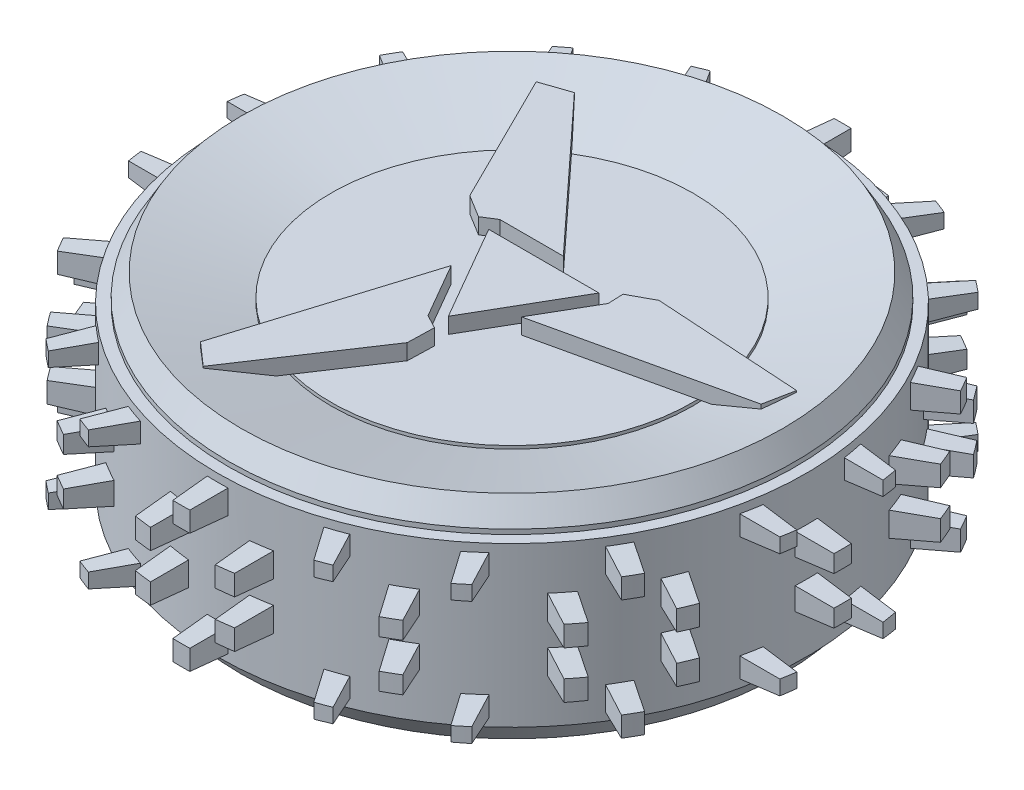
SolidWorks part; units mm, degrees
ref_plane "前视基准面" through (0, 0, 0) normal (0, 0, 1) x (1, 0, 0)
ref_plane "上视基准面" through (0, 0, 0) normal (0, 1, 0) x (1, 0, 0)
ref_plane "右视基准面" through (0, 0, 0) normal (1, 0, 0) x (0, 0, -1)
other "Configuration Table"
sketch "草图1" plane through (0, 0, 0) normal (0, 1, 0) x (1, 0, 0)
  circle A0 centre (0, 0) radius 90
  dimension "D1" = 180
extrude "凸台-拉伸1" add sketch "草图1" along normal mid plane 67.5
chamfer "倒角1" distance 7 angle 30 1 edges at (0, 33.75, 90)
chamfer "倒角2" distance 7 angle 30 1 edges at (0, -33.75, 90)
sketch "草图2" plane through (0, 0, 0) normal (0, 1, 0) x (1, 0, 0)
  circle A0 centre (0, 0) radius 93.5
  dimension "D1" = 187
extrude "凸台-拉伸2" add sketch "草图2" along normal mid plane 50.5
ref_plane "基准面1" through (0, 0, 80) normal (0, 0, 1) x (1, 0, 0)
ref_plane "基准面2" through (0, 0, 110) normal (0, 0, 1) x (1, 0, 0)
sketch "草图4" plane through (0, 0, 80) normal (0, 0, 1) x (1, 0, 0)
  line L0 (0, -55) -> (0, 55) construction
  line L1 (-4, 23.5) -> (4, 23.5)
  line L2 (-4, 23.5) -> (-4, 14.5)
  line L3 (-4, 14.5) -> (4, 14.5)
  line L4 (4, 23.5) -> (4, 14.5)
  line L5 (-17, 12) -> (-9, 12)
  line L6 (-17, 12) -> (-17, 3)
  line L7 (-17, 3) -> (-9, 3)
  line L8 (-9, 12) -> (-9, 3)
  line L9 (9, 12) -> (9, 3)
  line L10 (17, 3) -> (9, 3)
  line L11 (17, 12) -> (17, 3)
  line L12 (17, 12) -> (9, 12)
  line L13 (55, 0) -> (-55, 0) construction
  line L14 (17, -12) -> (9, -12)
  line L15 (17, -12) -> (17, -3)
  line L16 (17, -3) -> (9, -3)
  line L17 (9, -12) -> (9, -3)
  line L18 (-9, -12) -> (-9, -3)
  line L19 (-17, -3) -> (-9, -3)
  line L20 (-17, -12) -> (-17, -3)
  line L21 (-17, -12) -> (-9, -12)
  line L22 (4, -23.5) -> (4, -14.5)
  line L23 (-4, -14.5) -> (4, -14.5)
  line L24 (-4, -23.5) -> (-4, -14.5)
  line L25 (-4, -23.5) -> (4, -23.5)
  point P29 (0, 14.5)
  dimension "D1" = 6
  dimension "D2" = 24
  dimension "D3" = 34
  dimension "D4" = 18
  dimension "D5" = 47
extrude "凸台-拉伸3" add sketch "草图4" along normal mid plane 50.5 draft 3
ref_plane "基准面3" through (80, 0, 0) normal (1, 0, 0) x (0, 0, -1)
sketch "草图5" plane through (80, 0, 0) normal (1, 0, 0) x (0, 0, -1)
  line L0 (0, 55) -> (0, -55) construction
  line L1 (-20, 23.5) -> (-12, 23.5)
  line L2 (-20, 23.5) -> (-20, 15.5742)
  line L3 (-20, 15.5742) -> (-12, 15.5742)
  line L4 (-12, 23.5) -> (-12, 15.5742)
  line L9 (-4.5, 12) -> (4.5, 12)
  line L10 (-4.5, 12) -> (-4.5, 3)
  line L11 (-4.5, 3) -> (4.5, 3)
  line L12 (4.5, 12) -> (4.5, 3)
  line L13 (12, 23.5) -> (12, 15.5742)
  line L14 (20, 15.5742) -> (12, 15.5742)
  line L15 (20, 23.5) -> (20, 15.5742)
  line L16 (20, 23.5) -> (12, 23.5)
  line L17 (55, 0) -> (-55, 0) construction
  line L18 (20, -23.5) -> (12, -23.5)
  line L19 (20, -23.5) -> (20, -15.5742)
  line L20 (20, -15.5742) -> (12, -15.5742)
  line L21 (12, -23.5) -> (12, -15.5742)
  line L22 (4.5, -12) -> (4.5, -3)
  line L23 (-4.5, -3) -> (4.5, -3)
  line L24 (-4.5, -12) -> (-4.5, -3)
  line L25 (-4.5, -12) -> (4.5, -12)
  line L26 (-12, -23.5) -> (-12, -15.5742)
  line L27 (-20, -15.5742) -> (-12, -15.5742)
  line L28 (-20, -23.5) -> (-20, -15.5742)
  line L29 (-20, -23.5) -> (-12, -23.5)
  point P28 (0, 12)
  dimension "D1" = 40
  dimension "D2" = 47
  dimension "D3" = 6
  dimension "D4" = 24
  dimension "D5" = 24
extrude "凸台-拉伸4" add sketch "草图5" along normal mid plane 50.5 draft 4
pattern_circular "阵列(圆周)1" count 6 over 360 about axis through (0, 0, 0) along (0, 1, 0) of "凸台-拉伸4"
pattern_circular "阵列(圆周)2" count 6 over 360 about axis through (0, 0, 0) along (0, 1, 0) of "凸台-拉伸3"
sketch "草图6" plane through (0, 0, 0) normal (0, 1, 0) x (1, 0, 0)
  circle A0 centre (0, 0) radius 105
  circle A1 centre (0, 0) radius 115
  dimension "D1" = 210
  dimension "D2" = 10
extrude "切除-拉伸1" cut sketch "草图6" against normal through all and the other way through all
ref_plane "基准面4" through (0, -26.75, 0) normal (0, -1, 0) x (-1, 0, 0)
sketch "草图7" plane through (0, 0, 0) normal (0, 0, 1) x (1, 0, 0)
  line L0 (-85.9585, 33.75) -> (-57.5, 25.75)
  line L1 (-57.5, 25.75) -> (-57.5, 26.75)
  line L2 (-57.5, 26.75) -> (57.5, 26.75) construction
  line L3 (0, 26.75) -> (0, 33.75)
  line L4 (85.9585, 33.75) -> (-85.9585, 33.75) construction
  line L5 (0, -37.125) -> (0, 37.125) construction
  line L6 (57.5, 25.75) -> (57.5, 26.75) construction
  line L7 (85.9585, 33.75) -> (57.5, 25.75) construction
  line L8 (-85.9585, 33.75) -> (0, 33.75)
  line L9 (-57.5, 26.75) -> (0, 26.75)
  dimension "D1" = 7
  dimension "D2" = 1
  dimension "D3" = 115
revolve "切除-旋转1" cut sketch "草图7" angle 360 about L3
sketch "草图8" plane through (0, 26.75, 0) normal (0, 1, 0) x (1, 0, 0)
  line L0 (-17.5, 10.1036) -> (17.5, 10.1036)
  line L1 (17.5, 10.1036) -> (0, -20.2073)
  line L2 (0, -20.2073) -> (-17.5, 10.1036)
  line L3 (0, 0) -> (-17.5, 10.1036) construction
  line L4 (0, 0) -> (17.5, 10.1036) construction
  line L5 (0, 0) -> (0, -20.2073) construction
  line L6 (-18.4387, 14.5799) -> (1.715, 14.5799)
  line L7 (1.715, 14.5799) -> (-41.4802, 61.2865)
  line L8 (-41.4802, 61.2865) -> (-50.5383, 58.2184)
  line L9 (-50.5383, 58.2184) -> (-29.7781, 16.3754)
  line L10 (-29.7781, 16.3754) -> (-22.596, 11.9557)
  line L11 (-22.596, 11.9557) -> (-18.4387, 14.5799)
  line L12 (21.6519, 13.5909) -> (21.8459, 8.6784)
  line L13 (21.8459, 8.6784) -> (11.769, -8.7752)
  line L14 (11.769, -8.7752) -> (73.8157, 5.2797)
  line L15 (73.8157, 5.2797) -> (75.6878, 14.6583)
  line L16 (75.6878, 14.6583) -> (29.0706, 17.6008)
  line L17 (29.0706, 17.6008) -> (21.6519, 13.5909)
  line L18 (0.9441, -25.5465) -> (-3.4072, -23.2583)
  line L19 (-3.4072, -23.2583) -> (-13.4841, -5.8047)
  line L20 (-13.4841, -5.8047) -> (-32.3355, -66.5662)
  line L21 (-32.3355, -66.5662) -> (-25.1494, -72.8767)
  line L22 (-25.1494, -72.8767) -> (0.7075, -33.9763)
  line L23 (0.7075, -33.9763) -> (0.9441, -25.5465)
  point P5 (0, 10.1036)
  point P27 (0, 0)
  dimension "D1" = 35
  dimension "D2" = 3
extrude "凸台-拉伸5" add sketch "草图8" along normal blind 5
mirror "镜向1" about plane through (0, 0, 0) normal (0, 1, 0) of "凸台-拉伸5", "切除-旋转1"
sketch "草图9" plane through (0, -26.75, 0) normal (0, -1, 0) x (1, 0, 0)
  circle A0 centre (0, 0) radius 24.5
  circle A1 centre (0, 0) radius 30
  dimension "D1" = 49
  dimension "D2" = 60
extrude "切除-拉伸2" cut sketch "草图9" against normal blind 6 and the other way through all
sketch "草图10" plane through (0, -26.75, 0) normal (0, -1, 0) x (1, 0, 0)
  circle A0 centre (0, 0) radius 24.5
  circle A1 centre (0, 0) radius 24.5 construction
extrude "切除-拉伸3" cut sketch "草图10" along normal through all
sketch "草图11" plane through (0, -26.75, 0) normal (0, -1, 0) x (1, 0, 0)
  circle A0 centre (0, 0) radius 20 construction
  circle A1 centre (0, 20) radius 2
  circle A2 centre (17.3205, 10) radius 2
  circle A3 centre (17.3205, -10) radius 2
  circle A4 centre (0, -20) radius 2
  circle A5 centre (-17.3205, -10) radius 2
  circle A6 centre (-17.3205, 10) radius 2
  point P18 (0, 0)
  dimension "D1" = 40
  dimension "D2" = 4
  dimension "D3" = 6
extrude "切除-拉伸4" cut sketch "草图11" against normal blind 12
hole_wizard "M6 螺纹孔1" positions "3D草图1" profile "草图12" tap size "M6" standard "GB"
sketch3d "3D草图1"
  circle A0 centre (0, -26.75, 20) radius 2 construction
  circle A1 centre (-17.3205, -26.75, 10) radius 2 construction
  circle A2 centre (-17.3205, -26.75, -10) radius 2 construction
  circle A3 centre (0, -26.75, -20) radius 2 construction
  circle A4 centre (17.3205, -26.75, -10) radius 2 construction
  circle A5 centre (17.3205, -26.75, 10) radius 2 construction
  point P0 (0, -26.75, 20)
  point P2 (-17.3205, -26.75, 10)
  point P4 (-17.3205, -26.75, -10)
  point P6 (0, -26.75, -20)
  point P8 (17.3205, -26.75, -10)
  point P10 (17.3205, -26.75, 10)
  point P15 (0, -28.75, 20)
  point P19 (-17.3205, -28.75, 10)
  point P23 (-17.3205, -28.75, -10)
  point P26 (0, -28.75, -20)
  point P31 (17.3205, -28.75, -10)
  point P35 (17.3205, -28.75, 10)
sketch "草图12" plane through (0, -26.75, 20) normal (1, 0, 0) x (0, 0, -1)
  line L0 (0, 0) -> (0, 13.5022)
  line L1 (0, 13.5022) -> (2.5, 12)
  line L2 (2.5, 12) -> (2.5, 0)
  line L5 (2.5, 0) -> (0, 0)
  line L10 (0, 13.5022) -> (-2.5, 12) construction
  line L11 (0, -6.35) -> (0, 107.95) construction
  dimension "螺纹孔钻头直径" = 5
  dimension "螺纹孔钻头深度" = 12
  dimension "导头角度" = 118
cosmetic thread "孔螺蚊线1" parameters "D1"=12, "D2"=6
cosmetic thread "孔螺蚊线2" parameters "D1"=12, "D2"=6
cosmetic thread "孔螺蚊线3" parameters "D1"=12, "D2"=6
cosmetic thread "孔螺蚊线4" parameters "D1"=12, "D2"=6
cosmetic thread "孔螺蚊线5" parameters "D1"=12, "D2"=6
cosmetic thread "孔螺蚊线6" parameters "D1"=12, "D2"=6
sketch "草图13" plane through (0, -26.75, 0) normal (0, -1, 0) x (1, 0, 0)
  arc A0 (-13.0961, 15.116) -> (-6.7921, 18.8114) centre (0, 0) cw construction
  arc A1 (-7.8109, 21.6331) -> (-15.0605, 17.3833) centre (0, 0) ccw
  arc A2 (-5.7732, 15.9897) -> (-11.1317, 12.8486) centre (0, 0) ccw
  arc A3 (-5.7732, 15.9897) -> (-7.8109, 21.6331) centre (-6.7921, 18.8114) ccw
  arc A4 (-15.0605, 17.3833) -> (-11.1317, 12.8486) centre (-13.0961, 15.116) ccw
  circle A5 centre (0, 0) radius 20 construction
  point P3 (-10.1143, 17.254)
  dimension "D1" = 6
extrude "凸台-拉伸6" add sketch "草图13" along normal blind 20
sketch "草图14" plane through (0, -26.75, 0) normal (0, -1, 0) x (1, 0, 0)
  line L0 (-11.6314, 19.8421) -> (0, 0) construction
  circle A0 centre (-17.3205, 10) radius 3.1
  circle A3 centre (0, 20) radius 3.1
  circle A4 centre (17.3205, 10) radius 3.1
  circle A5 centre (17.3205, -10) radius 3.1
  circle A6 centre (0, -20) radius 3.1
  circle A7 centre (-17.3205, -10) radius 3.1
  arc A8 (-7.8109, 21.6331) -> (-15.0605, 17.3833) centre (0, 0) ccw construction
  circle A9 centre (0, 0) radius 24.5
  circle A10 centre (0, 0) radius 24.5
  dimension "D2" = 6.2
  dimension "D1" = 0
extrude "凸台-拉伸10" add sketch "草图14" along normal blind 5 separate body
sketch "草图15" plane through (0, -31.75, 0) normal (0, -1, 0) x (1, 0, 0)
  line L0 (-8.5971, 14.6659) -> (0, 0) construction
  line L1 (-18.0838, 17.7985) -> (-6.6962, 24.4739)
  line L2 (-18.0838, 17.7985) -> (-13.8358, 10.5518)
  line L3 (-6.6962, 24.4739) -> (-2.4482, 17.2272)
  line L4 (-13.8358, 10.5518) -> (-2.4482, 17.2272)
  circle A1 centre (0, 0) radius 24.5 construction
  arc A3 (-5.7732, 15.9897) -> (-11.1317, 12.8486) centre (0, 0) ccw construction
  point P6 (-8.142, 13.8895)
  point P9 (-12.39, 21.1362)
  dimension "D1" = 8.4
  dimension "D2" = 13.2
extrude "切除-拉伸6" cut sketch "草图15" against normal blind 5
fillet "圆角1" radius 2 4 edges at (-6.2381, -29.25, 23.6925) (-17.6258, -29.25, 17.0171) (-2.4482, -29.25, 17.2272) (-13.8358, -29.25, 10.5518)
sketch "草图16" plane through (0, -31.75, 0) normal (0, -1, 0) x (1, 0, 0)
  circle A0 centre (0, 0) radius 12
  dimension "D1" = 24
extrude "切除-拉伸7" cut sketch "草图16" against normal blind 5
mirror "镜向2" about plane through (0, -31.75, 0) normal (0, -1, 0) of bodies 123
mirror "镜向3" about plane through (0, -36.75, 0) normal (0, 1, 0) of bodies 124
